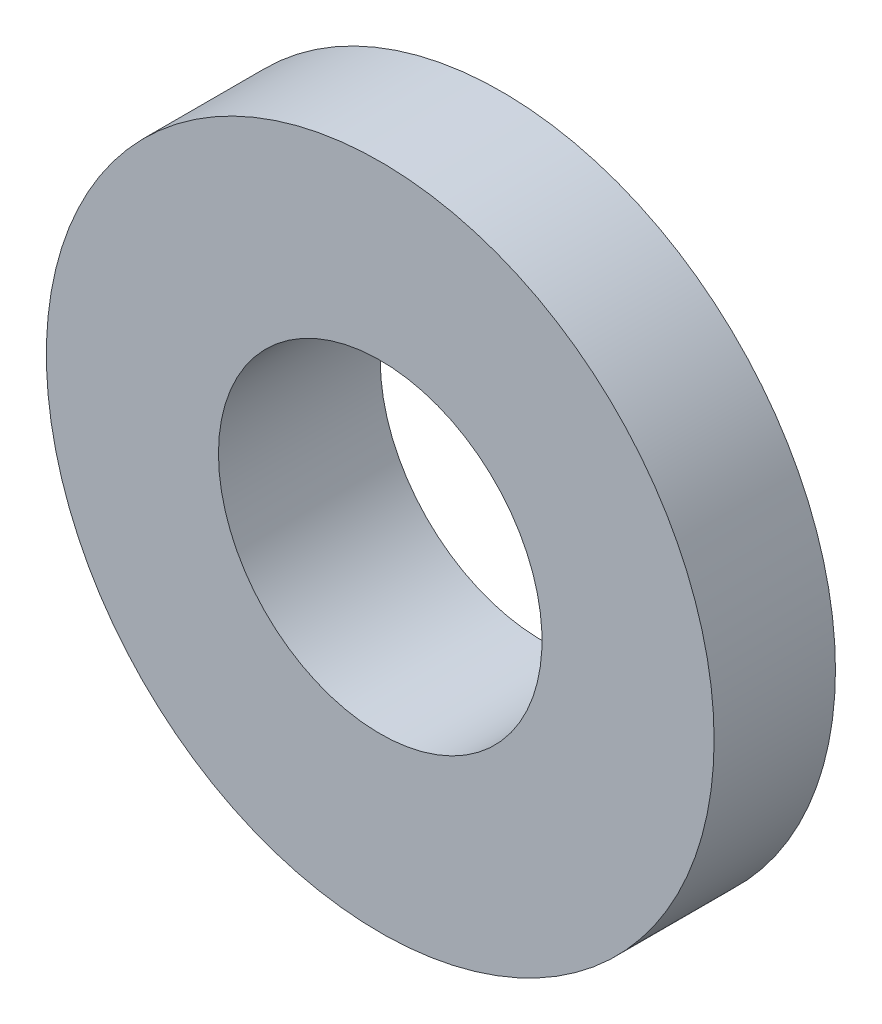
SolidWorks part; units mm, degrees
ref_plane "Front Plane" through (0, 0, 0) normal (0, 0, 1) x (1, 0, 0)
ref_plane "Top Plane" through (0, 0, 0) normal (0, 1, 0) x (1, 0, 0)
ref_plane "Right Plane" through (0, 0, 0) normal (1, 0, 0) x (0, 0, -1)
sketch "Sketch1" plane through (0, 0, 0) normal (0, 0, 1) x (1, 0, 0)
  circle A0 centre (0, 0) radius 8.255
  dimension "D1" = 16.51
extrude "Boss-Extrude1" add sketch "Sketch1" along normal blind 3
sketch "Sketch2" plane through (0, 0, 0) normal (0, 0, -1) x (-1, 0, 0)
  circle A0 centre (0, 0) radius 5
  dimension "D1" = 10
extrude "Boss-Extrude2" add sketch "Sketch2" along normal blind 1
sketch "Sketch3" plane through (0, 0, -1) normal (0, 0, -1) x (-1, 0, 0)
  circle A0 centre (0, 0) radius 4
  dimension "D1" = 8
extrude "Cut-Extrude1" cut sketch "Sketch3" against normal through all
